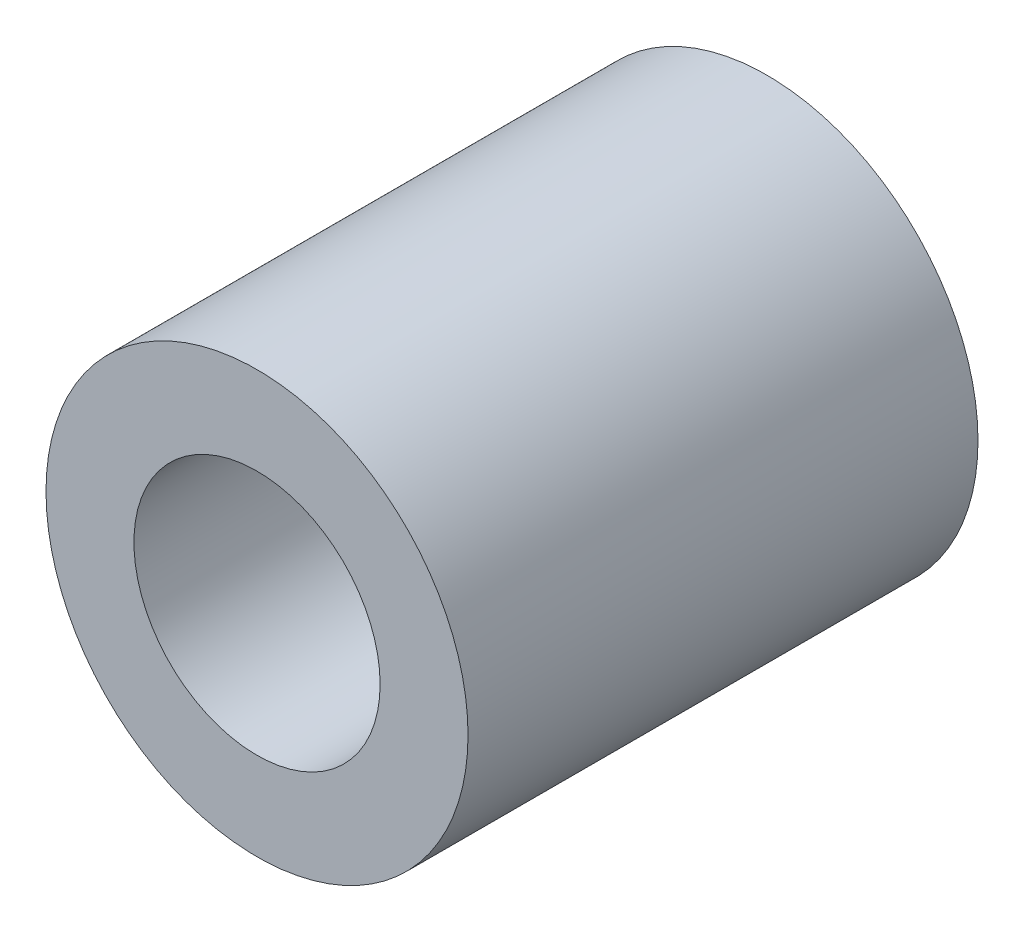
SolidWorks part; units mm, degrees
material "ABS"
ref_plane "前视基准面" through (0, 0, 0) normal (0, 0, 1) x (1, 0, 0)
ref_plane "上视基准面" through (0, 0, 0) normal (0, 1, 0) x (1, 0, 0)
ref_plane "右视基准面" through (0, 0, 0) normal (1, 0, 0) x (0, 0, -1)
sketch "草图1" plane through (0, 0, 0) normal (0, 0, 1) x (1, 0, 0)
  circle A0 centre (0, 0) radius 3.5
  circle A1 centre (0, 0) radius 6
extrude "凸台-拉伸1" add sketch "草图1" along normal blind 14.5
